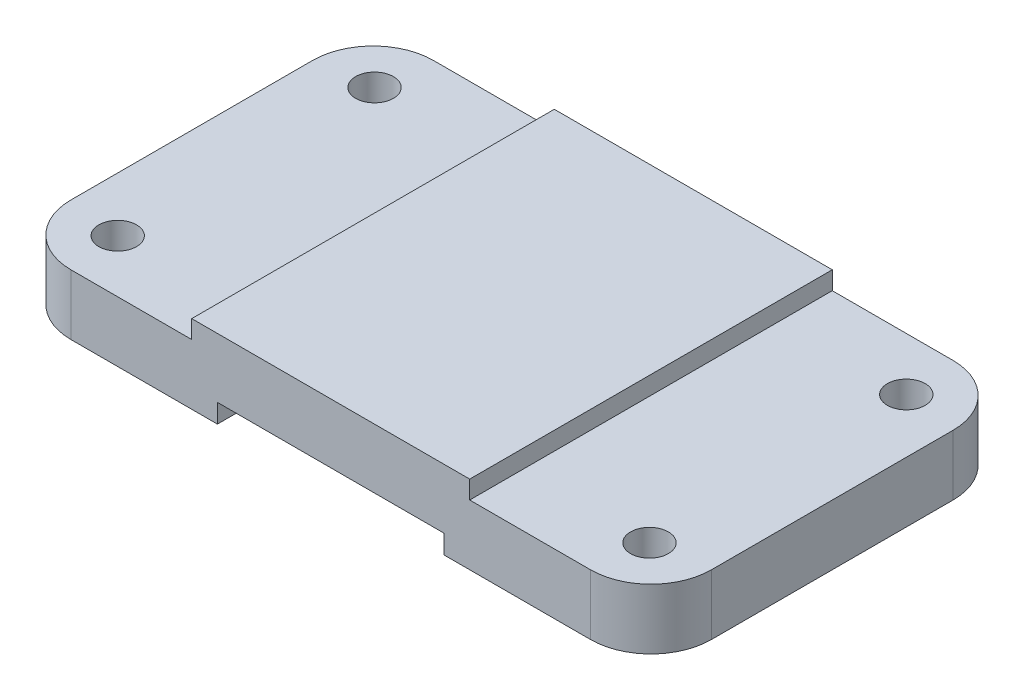
SolidWorks part; units mm, degrees
material "Gray Cast Iron"
ref_plane "Front Plane" through (0, 0, 0) normal (0, 0, 1) x (1, 0, 0)
ref_plane "Top Plane" through (0, 0, 0) normal (0, 1, 0) x (1, 0, 0)
ref_plane "Right Plane" through (0, 0, 0) normal (1, 0, 0) x (0, 0, -1)
sketch "Sketch1" plane through (0, 0, 0) normal (0, 1, 0) x (1, 0, 0)
  line L1 (12.7, 76.2) -> (121.92, 76.2)
  line L2 (0, 63.5) -> (0, 12.7)
  line L3 (12.7, 0) -> (121.92, 0)
  line L4 (134.62, 63.5) -> (134.62, 12.7)
  circle A0 centre (11.43, 65.0875) radius 3.9687
  circle A1 centre (123.19, 65.0875) radius 3.9687
  circle A2 centre (123.19, 11.1125) radius 3.9687
  circle A3 centre (11.43, 11.1125) radius 3.9688
  arc A4 (12.7, 76.2) -> (0, 63.5) centre (12.7, 63.5) ccw
  arc A5 (0, 12.7) -> (12.7, 0) centre (12.7, 12.7) ccw
  arc A6 (121.92, 0) -> (134.62, 12.7) centre (121.92, 12.7) ccw
  arc A7 (134.62, 63.5) -> (121.92, 76.2) centre (121.92, 63.5) ccw
  point P15 (0, 76.2)
  point P18 (0, 0)
  point P23 (134.62, 76.2)
  dimension "D3" = 7.9375
  dimension "D4" = 7.9375
  dimension "D5" = 7.9375
  dimension "D6" = 7.9375
  dimension "D15" = 12.7
  dimension "D16" = 12.7
  dimension "D1" = 134.62
  dimension "D2" = 76.2
  dimension "D7" = 111.76
  dimension "D8" = 111.76
  dimension "D9" = 0
  dimension "D10" = 11.43
  dimension "D11" = 53.975
  dimension "D12" = 53.975
  dimension "D13" = 11.1125
  dimension "D14" = 11.1125
extrude "Boss-Extrude1" add sketch "Sketch1" against normal blind 12.7
sketch "Sketch3" plane through (0, 0, 0) normal (0, 1, 0) x (1, 0, 0)
  line L0 (121.92, 76.2) -> (12.7, 76.2) construction
  line L1 (38.1, 76.2) -> (96.52, 76.2)
  line L2 (38.1, 76.2) -> (38.1, 0)
  line L3 (38.1, 0) -> (96.52, 0)
  line L4 (96.52, 76.2) -> (96.52, 0)
  line L5 (12.7, 0) -> (121.92, 0) construction
  line L6 (0, 63.5) -> (0, 12.7) construction
  dimension "D1" = 58.42
  dimension "D2" = 38.1
extrude "Boss-Extrude2" add sketch "Sketch3" along normal blind 3.81
sketch "Sketch4" plane through (0, -12.7, 0) normal (0, -1, 0) x (1, 0, 0)
  line L0 (12.7, 0) -> (121.92, 0) construction
  line L1 (43.4975, 0) -> (91.1225, 0)
  line L2 (43.4975, 0) -> (43.4975, -76.2)
  line L3 (43.4975, -76.2) -> (91.1225, -76.2)
  line L4 (91.1225, 0) -> (91.1225, -76.2)
  line L5 (121.92, -76.2) -> (12.7, -76.2) construction
  line L6 (0, -63.5) -> (0, -12.7) construction
  dimension "D1" = 47.625
  dimension "D2" = 43.4975
extrude "Cut-Extrude1" cut sketch "Sketch4" against normal blind 3.9624
